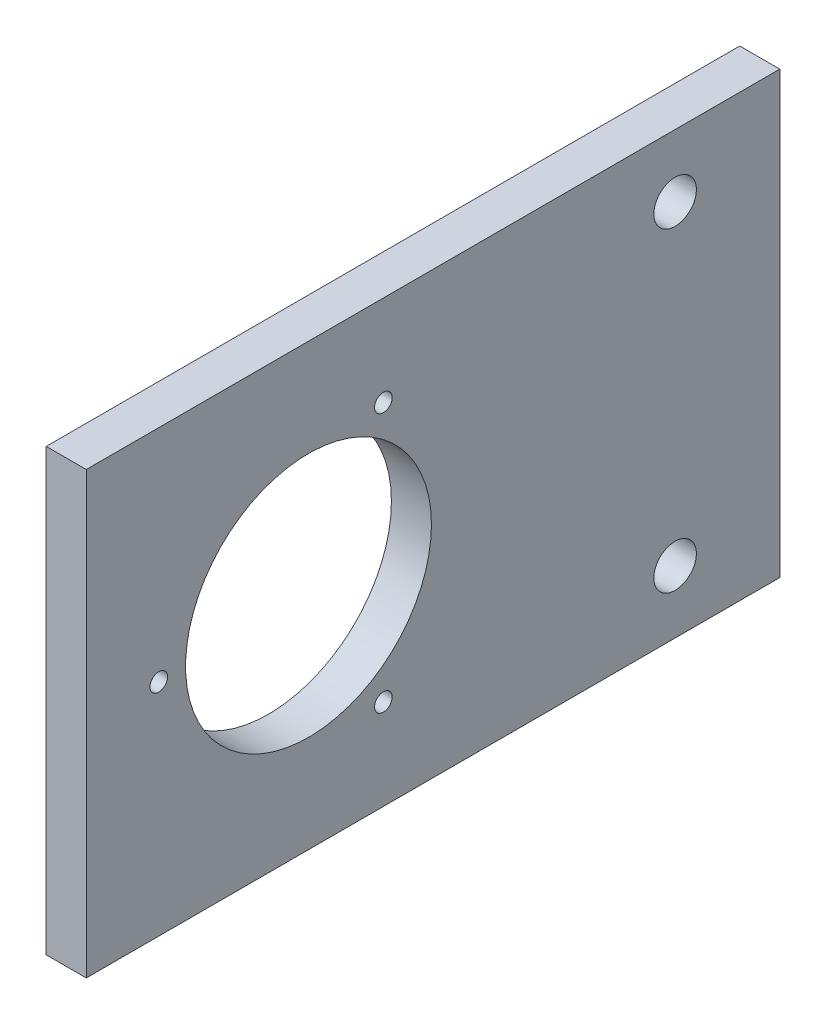
SolidWorks part; units mm, degrees
ref_plane "Front Plane" through (0, 0, 0) normal (1, 0, 0) x (0, 1, 0)
ref_plane "Top Plane" through (0, 0, 0) normal (0, 0, 1) x (0, 1, 0)
ref_plane "Right Plane" through (0, 0, 0) normal (0, 1, 0) x (-1, 0, 0)
sketch "Sketch1" plane through (0, 0, 0) normal (1, 0, 0) x (0, 1, 0)
  line L0 (0, 55) -> (0, -55) construction
  line L1 (-34.925, -55) -> (34.925, -55)
  line L2 (-34.925, -55) -> (-34.925, 55)
  line L3 (-34.925, 55) -> (34.925, 55)
  line L4 (34.925, -55) -> (34.925, 55)
  line L5 (-34.925, -55) -> (34.925, 55) construction
  line L6 (-34.925, 55) -> (34.925, -55) construction
  line L7 (-34.925, 19.75) -> (34.925, 19.75) construction
  line L8 (0, 19.75) -> (0, 43.5) construction
  line L9 (-25, -38.4) -> (25, -38.4) construction
  line L10 (-25, -38.4) -> (-25, 38.4) construction
  line L11 (-25, 38.4) -> (25, 38.4) construction
  line L12 (25, -38.4) -> (25, 38.4) construction
  line L13 (-25, -38.4) -> (25, 38.4) construction
  line L14 (-25, 38.4) -> (25, -38.4) construction
  line L15 (0, 19.75) -> (-20.5681, 7.875) construction
  line L16 (0, 19.75) -> (20.5681, 7.875) construction
  circle A5 centre (0, 19.75) radius 19.5
  circle A6 centre (-25, -38.4) radius 3.3731
  circle A7 centre (25, -38.4) radius 3.3731
  circle A8 centre (0, 43.5) radius 1.4
  circle A9 centre (20.5681, 7.875) radius 1.4
  circle A10 centre (-20.5681, 7.875) radius 1.4
  point P0 (0, 0)
  point P20 (0, 0)
  dimension "D5" = 120
  dimension "D6" = 2.8
  dimension "D7" = 23.75
  dimension "D8" = 39
  dimension "D11" = 23.75
  dimension "D12" = 6.7462
  dimension "D4" = 120
  dimension "D1" = 69.85
  dimension "D2" = 110
  dimension "D3" = 74.75
  dimension "D9" = 16.6
  dimension "D10" = 50
extrude "Boss-Extrude1" add sketch "Sketch1" along normal blind 6.35
